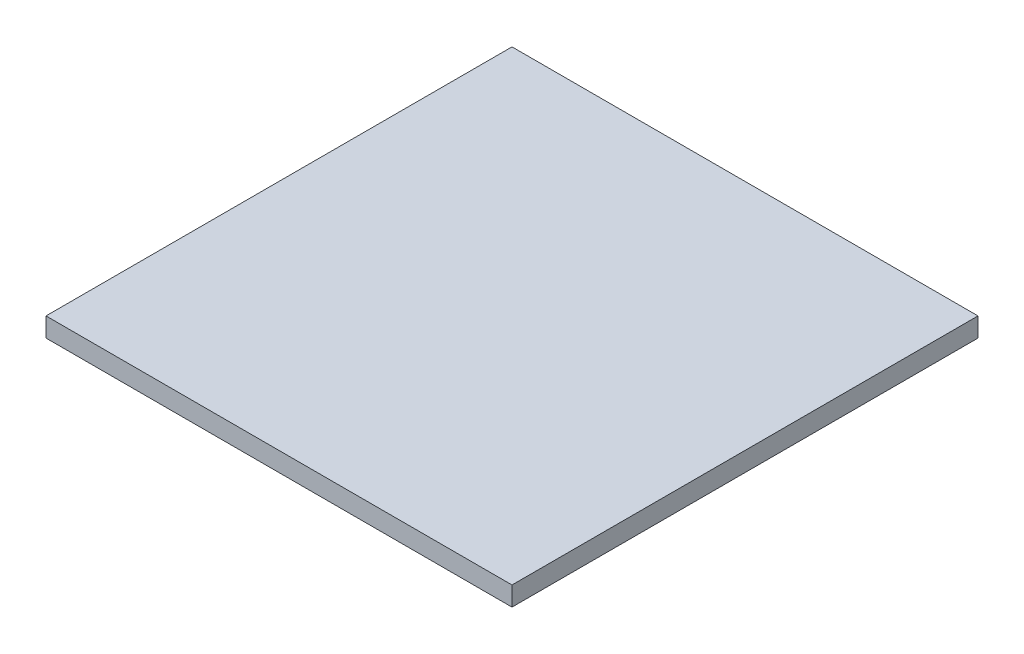
SolidWorks part; units mm, degrees
ref_plane "Front Plane" through (0, 0, 0) normal (0, 0, 1) x (1, 0, 0)
ref_plane "Top Plane" through (0, 0, 0) normal (0, 1, 0) x (1, 0, 0)
ref_plane "Right Plane" through (0, 0, 0) normal (1, 0, 0) x (0, 0, -1)
sketch "Sketch1" plane through (0, 0, 0) normal (0, 1, 0) x (1, 0, 0)
  line L1 (-38.5, 38.5) -> (38.5, 38.5)
  line L2 (-38.5, 38.5) -> (-38.5, -38.5)
  line L3 (-38.5, -38.5) -> (38.5, -38.5)
  line L4 (38.5, 38.5) -> (38.5, -38.5)
  dimension "D1" = 77
  dimension "D2" = 77
  dimension "D3" = 38.5
  dimension "D4" = 38.5
extrude "Boss-Extrude1" add sketch "Sketch1" along normal blind 3.175
